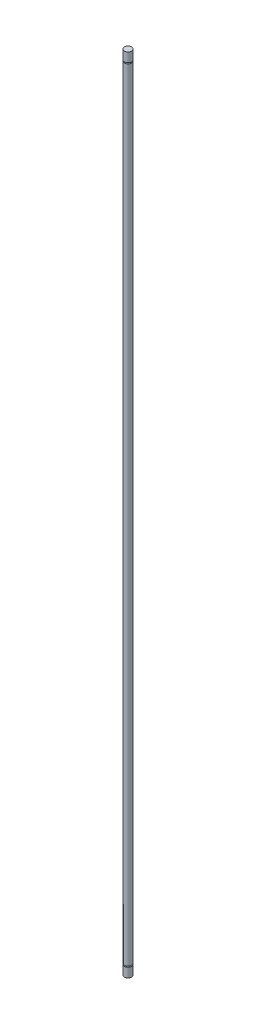
SolidWorks part; units mm, degrees
material "AISI 1010 Steel, hot rolled bar"
ref_plane "Front Plane" through (0, 0, 0) normal (0, 0, 1) x (1, 0, 0)
ref_plane "Top Plane" through (0, 0, 0) normal (0, 1, 0) x (1, 0, 0)
ref_plane "Right Plane" through (0, 0, 0) normal (1, 0, 0) x (0, 0, -1)
sketch "Sketch1" plane through (0, 0, 0) normal (0, 1, 0) x (1, 0, 0)
  circle A0 centre (0, 0) radius 2.3813
  dimension "D1" = 4.7625
extrude "Boss-Extrude1" add sketch "Sketch1" along normal mid plane 520.7
ref_plane "Plane6" through (0, -254, 0) normal (0, -1, 0) x (-1, 0, 0)
sketch "Sketch7" plane through (0, -254, 0) normal (0, -1, 0) x (-1, 0, 0)
  circle A0 centre (0, 0) radius 2.3813
  dimension "D1" = 4.7625
sketch "Sketch8" plane through (0, 0, 0) normal (1, 0, 0) x (0, 0, -1)
  line L0 (-2.6194, -254) -> (2.6194, -254) construction
  line L1 (1.5494, -253.6825) -> (3.2131, -253.6825)
  line L2 (1.5494, -253.6825) -> (1.5494, -254.3175)
  line L3 (1.5494, -254.3175) -> (3.2131, -254.3175)
  line L4 (3.2131, -253.6825) -> (3.2131, -254.3175)
  line L5 (1.5494, -253.6825) -> (3.2131, -254.3175) construction
  line L6 (1.5494, -254.3175) -> (3.2131, -253.6825) construction
  line L7 (2.3813, -260.35) -> (2.3813, 260.35) construction
  point P0 (2.3813, -254)
  dimension "D1" = 0.635
  dimension "D2" = 1.5494
sweep "Cut-Sweep1" cut profiles "Sketch8" path "Sketch7"
mirror "Mirror1" about plane through (0, 0, 0) normal (0, 1, 0) of "Cut-Sweep1"
